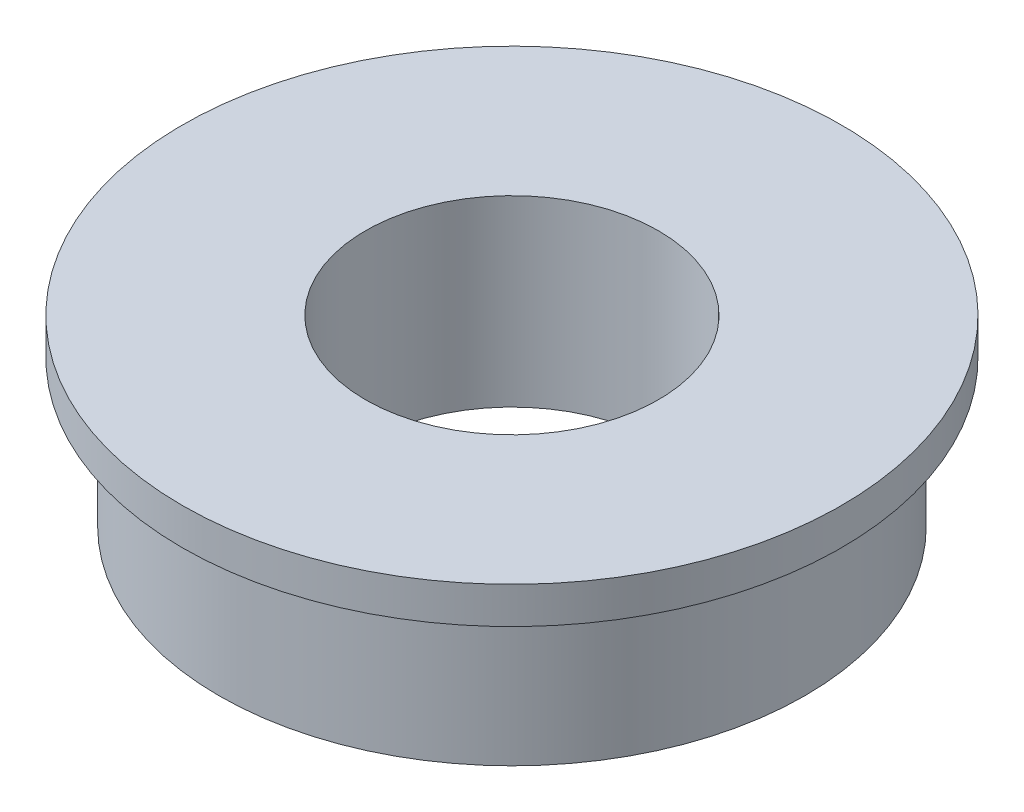
SolidWorks part; units mm, degrees
material "AISI 1035 钢 (SS)"
ref_plane "前视基准面" through (0, 0, 0) normal (0, 0, 1) x (1, 0, 0)
ref_plane "上视基准面" through (0, 0, 0) normal (0, 1, 0) x (1, 0, 0)
ref_plane "右视基准面" through (0, 0, 0) normal (1, 0, 0) x (0, 0, -1)
sketch "草图1" plane through (0, 0, 0) normal (0, 1, 0) x (1, 0, 0)
  circle A0 centre (0, 0) radius 4
  circle A1 centre (0, 0) radius 8
  dimension "D1" = 8
  dimension "D2" = 16
extrude "凸台-拉伸1" add sketch "草图1" along normal blind 4
sketch "草图2" plane through (0, 4, 0) normal (0, 1, 0) x (1, 0, 0)
  circle A0 centre (0, 0) radius 9
  circle A1 centre (0, 0) radius 4
  dimension "D1" = 18
extrude "凸台-拉伸2" add sketch "草图2" along normal blind 1
